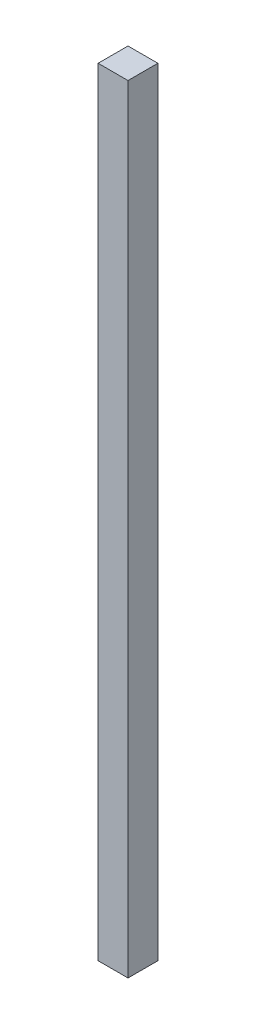
SolidWorks part; units mm, degrees
ref_plane "Plan de face" through (0, 0, 0) normal (0, 0, 1) x (1, 0, 0)
ref_plane "Plan de dessus" through (0, 0, 0) normal (0, 1, 0) x (1, 0, 0)
ref_plane "Plan de droite" through (0, 0, 0) normal (1, 0, 0) x (0, 0, -1)
sketch "Esquisse1" plane through (0, 0, 0) normal (0, 0, 1) x (1, 0, 0)
  line L1 (-21.9867, 13.5278) -> (-11.9867, 13.5278)
  line L2 (-21.9867, 13.5278) -> (-21.9867, -246.4722)
  line L3 (-21.9867, -246.4722) -> (-11.9867, -246.4722)
  line L4 (-11.9867, 13.5278) -> (-11.9867, -246.4722)
  dimension "D1" = 10
  dimension "D2" = 260
extrude "Boss.-Extru.1" add sketch "Esquisse1" along normal blind 10
equation "\"AA\"=31.7778"
equation "\"D2@Esquisse1\"= \"LargeurBoite\" - 20"
equation "\"EpaisseurPlaque\"= 3"
equation "\"ProfondeurBoite\"=460"
equation "\"LongueurSyphon\"=270"
equation "\"LargeurSyphon\"=120"
equation "\"HauteurCoteDroit\"= 490"
equation "\"HauteurCoteGauche\"= 540"
equation "\"HauteurSolSyphon\"= 300"
equation "\"HauteurSyphon\"=\"HauteurCoteGauche\"-\"HauteurSolSyphon\""
equation "\"LargeurDroite\"=10"
equation "\"LargeurGauche\"=150"
equation "\"LargeurBoite\"= \"LargeurDroite\" + \"LargeurGauche\" + \"LargeurSyphon\""
